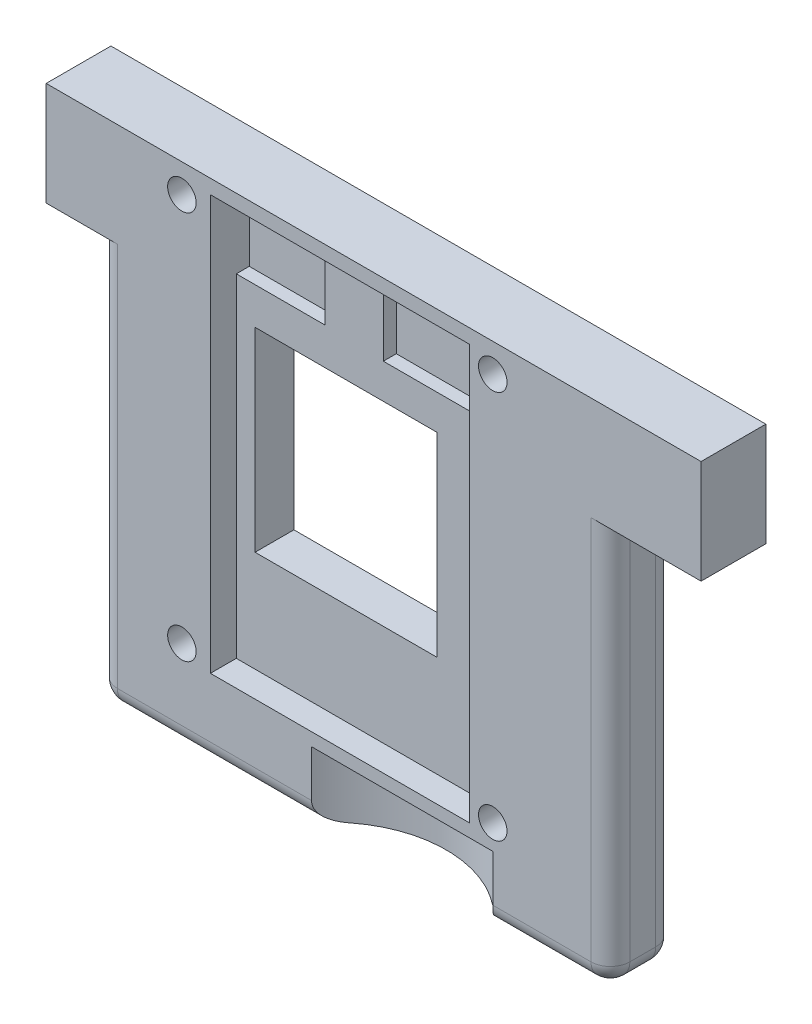
SolidWorks part; units mm, degrees
ref_plane "Front Plane" through (0, 0, 0) normal (0, 0, 1) x (1, 0, 0)
ref_plane "Top Plane" through (0, 0, 0) normal (0, 1, 0) x (1, 0, 0)
ref_plane "Right Plane" through (0, 0, 0) normal (1, 0, 0) x (0, 0, -1)
sketch "Sketch1" plane through (0, 0, 0) normal (0, 0, 1) x (1, 0, 0)
  line L0 (33.8069, 3.0603) -> (4.0069, 3.0603) construction
  line L1 (26.6969, -18.9397) -> (6.9169, -18.9397)
  line L2 (26.6969, -18.9397) -> (26.6969, 3.0603)
  line L3 (26.6969, 3.0603) -> (6.9169, 3.0603)
  line L4 (6.9169, -18.9397) -> (6.9169, 3.0603)
  line L5 (26.8069, -4.2397) -> (26.8069, -18.9397) construction
  line L6 (6.8069, -18.9397) -> (6.8069, -4.2397) construction
  line L9 (28.8069, -18.9397) -> (32.9069, -18.9397) construction
  dimension "D1" = 0.11
  dimension "D2" = 0.11
extrude "Boss-Extrude1" add sketch "Sketch1" along normal blind 2.5
sketch "Sketch2" plane through (0, 0, 2.5) normal (0, 0, 1) x (1, 0, 0)
  circle A0 centre (22.1562, -0.44) radius 0.55
  arc A1 (21.5562, -0.44) -> (22.7562, -0.44) centre (22.1562, -0.44) ccw construction
  circle A2 centre (22.1562, -15.44) radius 0.55
  circle A3 centre (10.1562, -15.44) radius 0.55
  circle A4 centre (10.1562, -0.44) radius 0.55
  arc A5 (21.5562, -15.44) -> (22.7562, -15.44) centre (22.1562, -15.44) ccw construction
  arc A6 (9.5562, -15.44) -> (10.7562, -15.44) centre (10.1562, -15.44) ccw construction
  arc A7 (9.5562, -0.44) -> (10.7562, -0.44) centre (10.1562, -0.44) ccw construction
  dimension "D1" = 1.1
extrude "Cut-Extrude1" cut sketch "Sketch2" against normal up to surface (2.5 mm away) up to face at (16.8069, -7.9397, 0)
sketch "Sketch3" plane through (0, 0, 2.5) normal (0, 0, 1) x (1, 0, 0)
  line L1 (18.9952, -11.9808) -> (11.9809, -11.9808)
  line L2 (18.9952, -11.9808) -> (18.9952, -4.4613)
  line L3 (18.9952, -4.4613) -> (11.9809, -4.4613)
  line L4 (11.9809, -11.9808) -> (11.9809, -4.4613)
extrude "Cut-Extrude2" cut sketch "Sketch3" against normal blind 2.5
sketch "Sketch4" plane through (0, 0, 2.5) normal (0, 0, 1) x (1, 0, 0)
  line L0 (11.6499, -16.3897) -> (20.8638, -16.3897) construction
  line L1 (21.2569, -15.8897) -> (11.2569, -15.8897)
  line L2 (21.2569, -15.8897) -> (21.2569, 0.1103)
  line L3 (21.2569, 0.1103) -> (11.2569, 0.1103)
  line L4 (11.2569, -15.8897) -> (11.2569, 0.1103)
  line L5 (20.9217, 0.6103) -> (11.592, 0.6103) construction
  line L6 (21.7569, -13.0397) -> (21.7569, -2.8397) construction
  line L7 (10.7569, -2.8397) -> (10.7569, -13.0397) construction
  dimension "D1" = 0.5
  dimension "D2" = 0.5
  dimension "D3" = 0.5
  dimension "D4" = 0.5
extrude "Cut-Extrude3" cut sketch "Sketch4" against normal blind 1
sketch "Sketch5" plane through (0, 0, 1.5) normal (0, 0, 1) x (1, 0, 0)
  line L0 (21.2569, -15.8897) -> (21.2569, 0.1103) construction
  line L1 (21.2569, -3.1188) -> (16.9316, -3.1188)
  line L2 (21.2569, -3.1188) -> (21.2569, -0.3783)
  line L3 (21.2569, -0.3783) -> (16.9316, -0.3783)
  line L4 (16.9316, -3.1188) -> (16.9316, -0.3783)
  line L6 (11.2569, 0.1103) -> (11.2569, -15.8897) construction
  line L7 (11.2569, -3.0355) -> (14.6819, -3.0355)
  line L8 (11.2569, -3.0355) -> (11.2569, 0.1103)
  line L9 (11.2569, 0.1103) -> (14.6819, 0.1103)
  line L10 (14.6819, -3.0355) -> (14.6819, 0.1103)
  line L11 (21.2569, 0.1103) -> (11.2569, 0.1103) construction
extrude "Cut-Extrude4" cut sketch "Sketch5" against normal blind 0.5
sketch "Sketch6" plane through (0, -17.4897, 0) normal (0, -1, 0) x (1, 0, 0)
  circle A0 centre (18.6569, 5.25) radius 4.45
  arc A1 (22.1069, 5.25) -> (15.2069, 5.25) centre (18.6569, 5.25) ccw construction
  dimension "D1" = 1
extrude "Cut-Extrude5" cut sketch "Sketch6" against normal blind 1.1 and the other way blind 1.5
sketch "Sketch7" plane through (0, 3.0603, 0) normal (0, 1, 0) x (1, 0, 0)
  line L1 (26.6969, -2.5) -> (6.9169, -2.5)
  line L2 (26.6969, -2.5) -> (26.6969, 0)
  line L3 (26.6969, 0) -> (6.9169, 0)
  line L4 (6.9169, -2.5) -> (6.9169, 0)
extrude "Cut-Extrude6" cut sketch "Sketch7" against normal offset from surface (2.4 mm away) 0.4
sketch "Sketch8" plane through (0, 0, 2.5) normal (0, 0, 1) x (1, 0, 0)
  line L0 (6.9169, 0.6603) -> (6.9169, -18.9397) construction
  line L1 (26.6969, 0.6603) -> (30.1969, 0.6603)
  line L2 (26.6969, 0.6603) -> (26.6969, -3.3397)
  line L3 (26.6969, -3.3397) -> (30.1969, -3.3397)
  line L4 (30.1969, 0.6603) -> (30.1969, -3.3397)
  line L5 (6.9169, -3.3397) -> (4.9169, -3.3397)
  line L6 (6.9169, -3.3397) -> (6.9169, 0.6603)
  line L7 (6.9169, 0.6603) -> (4.9169, 0.6603)
  line L8 (4.9169, -3.3397) -> (4.9169, 0.6603)
  line L9 (26.6969, 0.6603) -> (6.9169, 0.6603) construction
  dimension "D1" = 4
  dimension "D2" = 3.5
  dimension "D3" = 2
extrude "Boss-Extrude2" add sketch "Sketch8" against normal up to surface (2.5 mm away) up to face at (22.7062, -0.44, 0)
fillet "Fillet1" radius 0.75 9 edges at (6.9169, -11.1397, 0) (6.9169, -11.1397, 2.5) (26.6969, -11.1397, 0) (26.6969, -11.1397, 2.5) (11.0376, -18.9397, 2.5) (24.4261, -18.9397, 2.5) (6.9169, -18.9397, 1.25) (16.8069, -18.9397, 0) (26.6969, -18.9397, 1.25)
